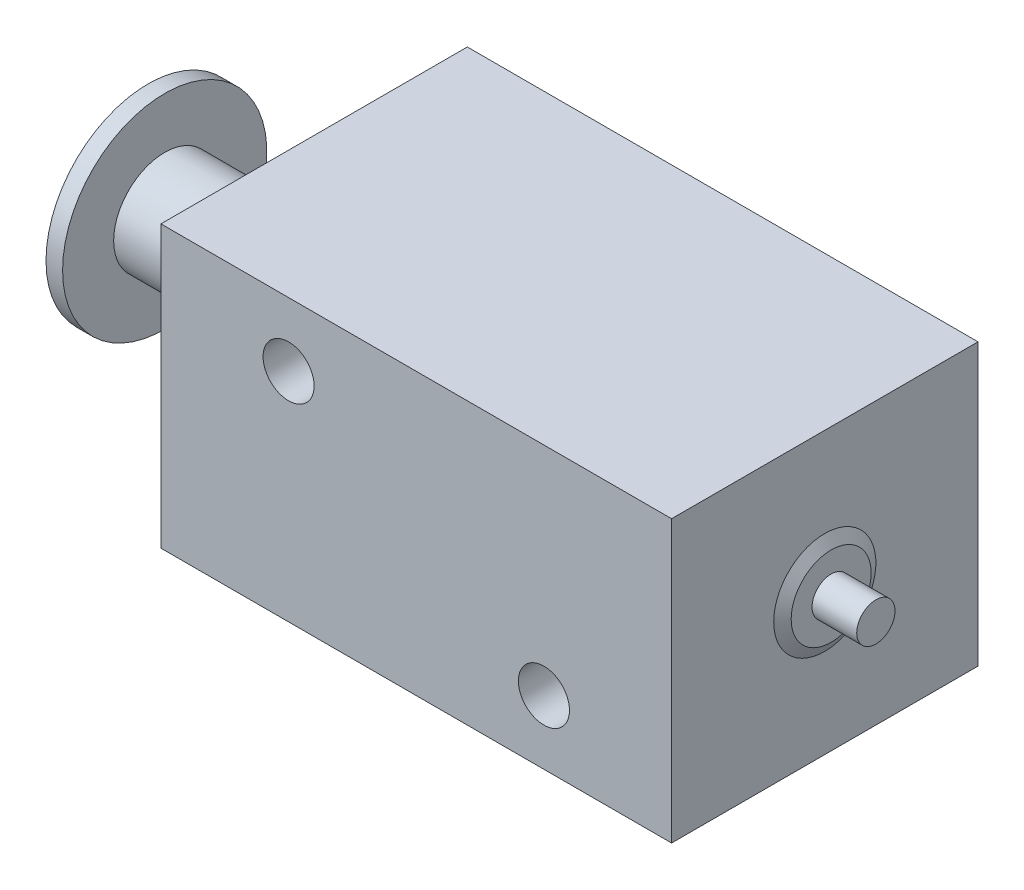
SolidWorks part; units mm, degrees
ref_plane "Front Plane" through (0, 0, 0) normal (0, 0, 1) x (1, 0, 0)
ref_plane "Top Plane" through (0, 0, 0) normal (0, 1, 0) x (1, 0, 0)
ref_plane "Right Plane" through (0, 0, 0) normal (1, 0, 0) x (0, 0, -1)
sketch "Sketch1" plane through (0, 0, 0) normal (0, 1, 0) x (1, 0, 0)
  line L0 (-10, -6) -> (10, 6) construction
  line L1 (-10, 6) -> (10, 6)
  line L2 (-10, 6) -> (-10, -6)
  line L3 (-10, -6) -> (10, -6)
  line L4 (10, 6) -> (10, -6)
  dimension "D1" = 12
  dimension "D2" = 20
extrude "Boss-Extrude1" add sketch "Sketch1" along normal mid plane 11
sketch "Sketch2" plane through (0, 0, 6) normal (0, 0, 1) x (1, 0, 0)
  line L0 (10, 5.5) -> (10, -5.5) construction
  circle A0 centre (5, -3) radius 1
  circle A1 centre (-5, 3) radius 1
  dimension "D5" = 2
  dimension "D1" = 3
  dimension "D2" = 3
  dimension "D3" = 5
  dimension "D4" = 10
extrude "Cut-Extrude1" cut sketch "Sketch2" against normal blind 3
sketch "Sketch3" plane through (0, 0, 0) normal (0, 1, 0) x (1, 0, 0)
  line L0 (12, 0) -> (12, 0.75)
  line L1 (12, 0.75) -> (10.25, 0.75)
  line L2 (10.25, 0.75) -> (10.25, 1.567)
  line L3 (10.25, 1.567) -> (10, 2)
  line L4 (10, -6) -> (10, 6) construction
  line L5 (10, 2) -> (-15.85, 2)
  line L6 (-15.85, 2) -> (-15.85, 4)
  line L7 (-15.85, 4) -> (-16.5, 4)
  line L8 (-16.5, 4) -> (-16.5, 2)
  line L9 (-16.5, 2) -> (-17.5, 2)
  line L10 (-17.5, 2) -> (-17.5, 0)
  line L11 (-17.5, 0) -> (12, 0)
  point P0 (12, 0)
  dimension "D1" = 2
  dimension "D2" = 2
  dimension "D3" = 4
  dimension "D4" = 0.65
  dimension "D5" = 29.5
  dimension "D6" = 1
  dimension "D7" = 0.75
  dimension "D8" = 0.25
  dimension "D9" = 30
revolve "Revolve1" add sketch "Sketch3" angle 360 about L11
